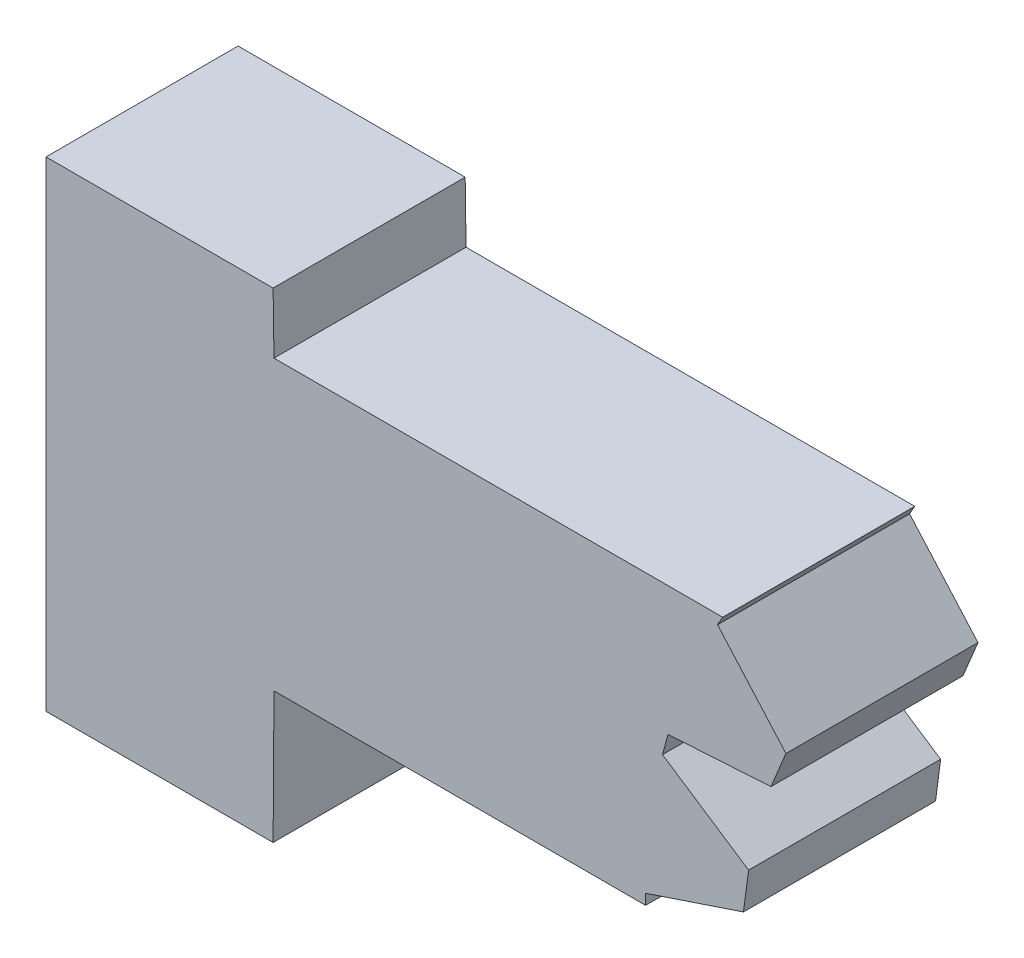
SolidWorks part; units mm, degrees
ref_plane "Front Plane" through (0, 0, 0) normal (0, 0, 1) x (1, 0, 0)
ref_plane "Top Plane" through (0, 0, 0) normal (0, 1, 0) x (1, 0, 0)
ref_plane "Right Plane" through (0, 0, 0) normal (1, 0, 0) x (0, 0, -1)
sketch "Sketch1" plane through (0, 0, 0) normal (0, 0, 1) x (1, 0, 0)
  line L0 (4.7478, 2.7448) -> (12.4871, 2.7448)
  line L1 (4.7478, 2.7448) -> (4.73, 0)
  line L2 (4.7478, 8.7448) -> (14.0928, 8.7448)
  line L3 (12.4871, 2.7448) -> (12.4871, 2.9629)
  line L4 (4.73, 0) -> (0, 0)
  line L5 (12.4871, 2.9629) -> (14.5257, 3.6448)
  line L6 (14.5257, 3.6448) -> (14.6321, 4.4531)
  line L7 (14.6321, 4.4531) -> (12.8395, 5.6394)
  line L8 (12.8395, 5.6394) -> (12.9523, 6.0607)
  line L9 (12.9523, 6.0607) -> (15.098, 6.1918)
  line L10 (15.098, 6.1918) -> (15.41, 6.9451)
  line L11 (15.41, 6.9451) -> (13.9855, 8.5549)
  line L12 (13.9855, 8.5549) -> (14.0928, 8.7448)
  line L13 (4.73, 10) -> (0, 10)
  line L14 (0, 0) -> (0, 10)
  line L15 (4.73, 10) -> (4.7478, 8.7448)
  dimension "D1" = 4.73
  dimension "D2" = 4.7478
  dimension "D3" = 1.2552
  dimension "D4" = 9.345
  dimension "D5" = 0.4362
  dimension "D6" = 2.1496
  dimension "D7" = 0.8153
  dimension "D8" = 0.2181
  dimension "D9" = 8.5549
  dimension "D10" = 6.9451
  dimension "D11" = 6.1918
  dimension "D12" = 6.0607
  dimension "D13" = 2.7448
  dimension "D14" = 5.6394
  dimension "D15" = 4.4531
  dimension "D16" = 3.6448
  dimension "D23" = 10
extrude "Boss-Extrude1" add sketch "Sketch1" along normal blind 4
equation "\"D4@Sketch1\"= \"ThumbLinkLengthMCP@Sketch1@thumbMovingBracketDown.SLDPRT\" - 10.7 'Toothed Mechanism"
